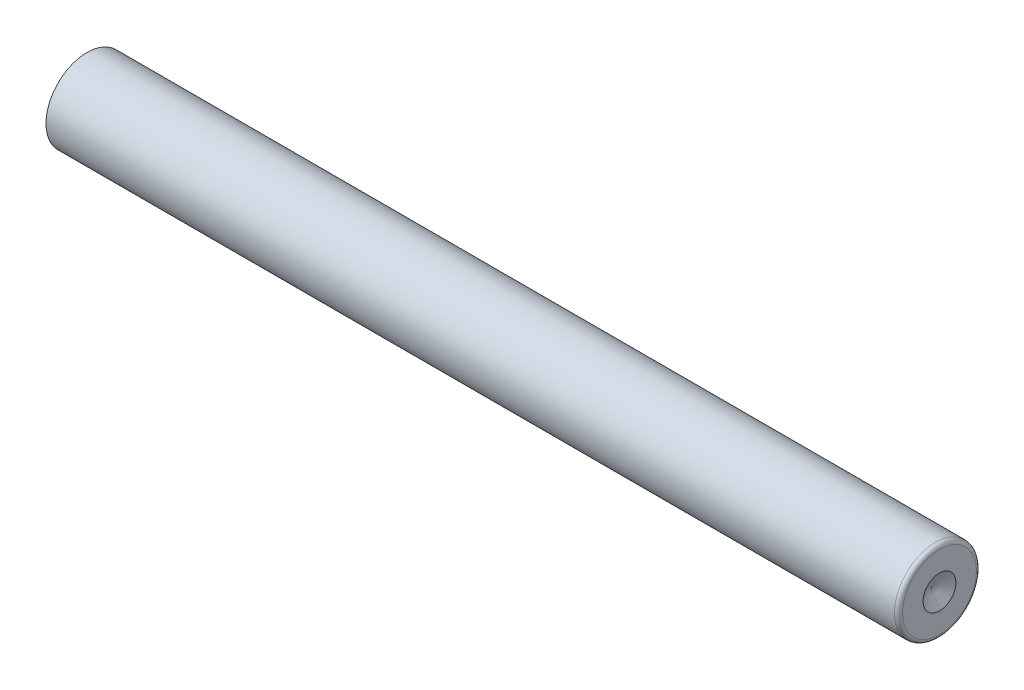
SolidWorks part; units mm, degrees
material "AISI 316 Barra de acero inoxidable recocido (SS)"
ref_plane "Alzado" through (0, 0, 0) normal (0, 0, 1) x (1, 0, 0)
ref_plane "Planta" through (0, 0, 0) normal (0, 1, 0) x (1, 0, 0)
ref_plane "Vista lateral" through (0, 0, 0) normal (1, 0, 0) x (0, 0, -1)
sketch "Croquis1" plane through (0, 0, 0) normal (0, 0, 1) x (1, 0, 0)
  line L1 (0, 0) -> (52, 0)
  line L2 (0, 0) -> (0, 2.5)
  line L3 (0, 2.5) -> (52, 2.5)
  line L4 (52, 0) -> (52, 2.5)
  dimension "D1" = 2.5
  dimension "D2" = 52
revolve "Revolución1" add sketch "Croquis1" angle 360 about L1
fillet "Redondeo1" radius 0.25 1 edges at (52, 0, 2.5)
sketch "Croquis3" plane through (0, 0, 0) normal (0, 0, 1) x (1, 0, 0)
  line L0 (52, 0) -> (51.5, 0)
  line L1 (52, -2.25) -> (52, 2.25) construction
  line L2 (51.5, 0) -> (52, 1)
  line L3 (52, 1) -> (52, 0)
  dimension "D1" = 0.5
  dimension "D2" = 1
revolve "Cortar-Revolución1" cut sketch "Croquis3" angle 360 about L0
